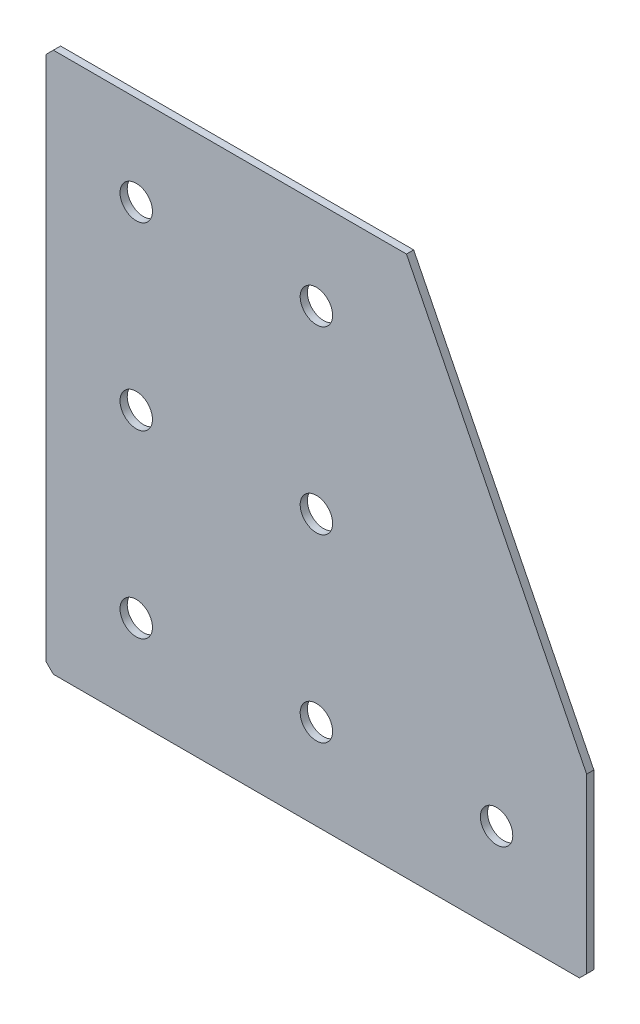
SolidWorks part; units mm, degrees
material "Простая углеродистая сталь"
ref_plane "Спереди(Плоскость XY)" through (0, 0, 0) normal (0, 0, 1) x (1, 0, 0)
ref_plane "Сверху(Плоскость XZ)" through (0, 0, 0) normal (0, 1, 0) x (1, 0, 0)
ref_plane "Справа(Плоскость ZY)" through (0, 0, 0) normal (1, 0, 0) x (0, 0, -1)
sketch "Эскиз1" plane through (0, 0, 0) normal (0, 0, -1) x (1, 0, 0)
  line L0 (0, 0) -> (0, 150)
  line L1 (0, 150) -> (150, 150)
  line L2 (150, 150) -> (150, 100)
  line L3 (150, 100) -> (100, 100) construction
  line L4 (100, 100) -> (100, 0) construction
  line L5 (100, 0) -> (0, 0)
  line L6 (150, 100) -> (100, 0)
  dimension "D1" = 150
  dimension "D2" = 50
  dimension "D3" = 100
extrude "Бобышка-Вытянуть1" add sketch "Эскиз1" along normal blind 2
hole_wizard "Отверстие с зазором M81" positions "Эскиз2" profile "Эскиз3" hole size "M8" standard "IS" end condition through all
sketch "Эскиз2" plane through (0, 0, -2) normal (0, 0, -1) x (1, 0, 0)
  line L0 (25, 0) -> (25, 150) construction
  line L1 (0, 0) -> (100, 0) construction
  line L2 (150, 150) -> (0, 150) construction
  line L3 (150, 125) -> (0, 125) construction
  line L4 (150, 100) -> (150, 150) construction
  line L5 (0, 150) -> (0, 0) construction
  point P0 (75, 125)
  point P2 (25, 125)
  point P4 (25, 75)
  point P6 (25, 25)
  point P21 (125, 125)
  point P24 (75, 75)
  point P26 (75, 25)
  dimension "D1" = 50
  dimension "D2" = 50
  dimension "D3" = 50
  dimension "D4" = 25
  dimension "D5" = 50
  dimension "D6" = 25
sketch "Эскиз3" plane through (75, -125, -2) normal (1, 0, 0) x (0, 1, 0)
  line L0 (0, 0) -> (0, 2)
  line L1 (0, 2) -> (4.5, 2)
  line L2 (4.5, 2) -> (4.5, 0)
  line L5 (4.5, 0) -> (0, 0)
  line L11 (0, -6.35) -> (0, 107.95) construction
  dimension "Диаметр сквозного отверстия" = 9
  dimension "Глубина сквозного отверстия" = 2
chamfer "Фаска1" distance 2 angle 45 3 edges at (0, 0, -1) (150, -150, -1) (0, -150, -1)
